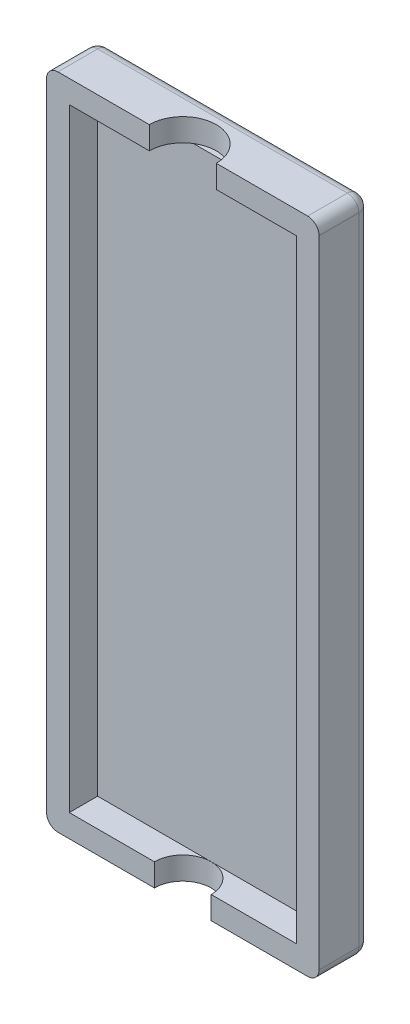
SolidWorks part; units mm, degrees
ref_plane "Front Plane" through (0, 0, 0) normal (0, 0, 1) x (1, 0, 0)
ref_plane "Top Plane" through (0, 0, 0) normal (0, 1, 0) x (1, 0, 0)
ref_plane "Right Plane" through (0, 0, 0) normal (1, 0, 0) x (0, 0, -1)
sketch "Sketch1" plane through (0, 0, 0) normal (0, 0, 1) x (1, 0, 0)
  line L1 (-12, 29) -> (12, 29)
  line L2 (-12, 29) -> (-12, -29)
  line L3 (-12, -29) -> (12, -29)
  line L4 (12, 29) -> (12, -29)
  line L5 (-12, 29) -> (12, -29) construction
  line L6 (-12, -29) -> (12, 29) construction
  point P0 (0, 0)
  dimension "D1" = 24
  dimension "D2" = 58
extrude "Boss-Extrude1" add sketch "Sketch1" along normal blind 2
sketch "Sketch2" plane through (0, 0, 2) normal (0, 0, 1) x (1, 0, 0)
  line L1 (-12, 29) -> (12, 29)
  line L2 (-12, 29) -> (-12, -29)
  line L3 (-12, -29) -> (12, -29)
  line L4 (12, 29) -> (12, -29)
  line L5 (-10, 27) -> (10, 27)
  line L6 (-10, 27) -> (-10, -27)
  line L7 (-10, -27) -> (10, -27)
  line L8 (10, 27) -> (10, -27)
  dimension "D1" = 2
  dimension "D2" = 2
  dimension "D3" = 2
  dimension "D4" = 2
extrude "Boss-Extrude2" add sketch "Sketch2" along normal blind 2.5
sketch "Sketch3" plane through (0, 27, 0) normal (0, -1, 0) x (1, 0, 0)
  line L0 (-12, 4.5) -> (12, 4.5) construction
  line L1 (-2.95, 4.5) -> (2.95, 4.5)
  arc A0 (-2.95, 4.5) -> (2.95, 4.5) centre (0, 4.5) ccw
  dimension "D1" = 5.9
extrude "Cut-Extrude1" cut sketch "Sketch3" against normal through all
sketch "Sketch4" plane through (0, -27, 0) normal (0, 1, 0) x (1, 0, 0)
  line L0 (-10, -4.5) -> (10, -4.5) construction
  line L1 (-2.5, -4.5) -> (2.5, -4.5)
  arc A0 (2.5, -4.5) -> (-2.5, -4.5) centre (0, -4.5) ccw
  dimension "D1" = 5
extrude "Cut-Extrude2" cut sketch "Sketch4" against normal through all
fillet "Fillet1" radius 1 8 edges at (12, -29, 2.25) (0, -29, 0) (-12, -29, 2.25) (-12, 0, 0) (-12, 29, 2.25) (12, 0, 0) (0, 29, 0) (12, 29, 2.25)
sketch "Sketch7" plane through (0, 0, 0) normal (0, 0, -1) x (-1, 0, 0)
  text T0 "Thermocouple" font "Centaur" height in points 8
extrude "Cut-Extrude4" cut sketch "Sketch7" against normal blind 1
sketch "Sketch9" plane through (0, 0, 0) normal (0, 0, -1) x (-1, 0, 0)
  text T0 "Meritus" font "Book Antiqua" height in points 8
extrude "Cut-Extrude5" cut sketch "Sketch9" against normal blind 1
